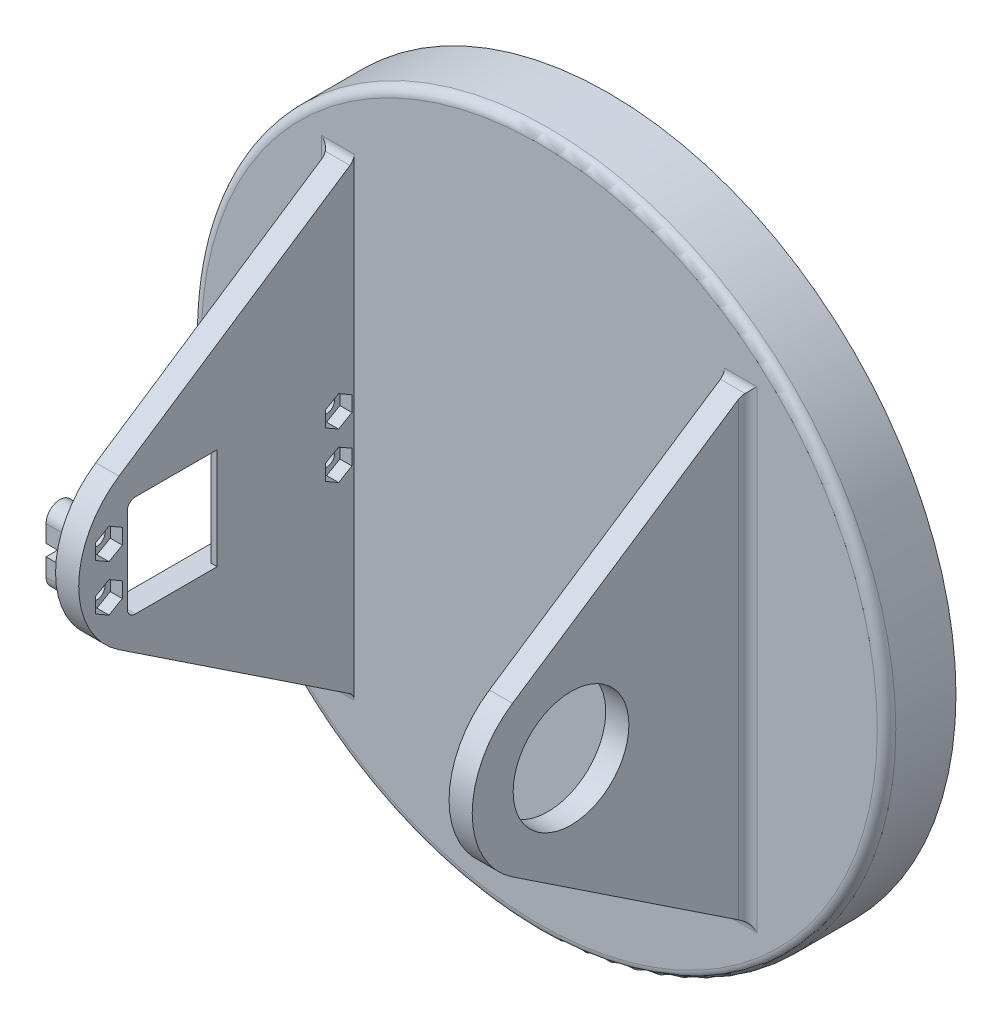
SolidWorks part; units mm, degrees
ref_plane "Front Plane" through (0, 0, 0) normal (0, 0, 1) x (1, 0, 0)
ref_plane "Top Plane" through (0, 0, 0) normal (0, 1, 0) x (1, 0, 0)
ref_plane "Right Plane" through (0, 0, 0) normal (1, 0, 0) x (0, 0, -1)
sketch "Sketch1" plane through (0, 0, 0) normal (0, 0, 1) x (1, 0, 0)
  circle A0 centre (0, 0) radius 75
  dimension "D1" = 150
extrude "Base Plate\\" add sketch "Sketch1" along normal blind 15
sketch "Sketch2" plane through (0, 0, 0) normal (0, 0, -1) x (-1, 0, 0)
  circle A0 centre (0, 0) radius 25 construction
  circle A1 centre (0, -25) radius 4.5
  circle A2 centre (-23.7764, -7.7254) radius 4.5
  circle A3 centre (-14.6946, 20.2254) radius 4.5
  circle A4 centre (14.6946, 20.2254) radius 4.5
  circle A5 centre (23.7764, -7.7254) radius 4.5
  point P16 (0, 0)
  dimension "D2" = 9
  dimension "D3" = 50
  dimension "D1" = 5
extrude "Drive Holes" cut sketch "Sketch2" against normal blind 10
chamfer "Chamfer1" distance 1 5 edges at (19.2764, -7.7254, 0) (10.1946, 20.2254, 0) (-19.1946, 20.2254, 0) (-28.2764, -7.7254, 0) (-4.5, -25, 0)
sketch "Sketch4" plane through (0, 0, 0) normal (1, 0, 0) x (0, 0, -1)
  line L0 (-15, 50) -> (-65.792, 16.2334)
  line L1 (-15, 75) -> (-15, -75) construction
  line L2 (-65.792, -16.2334) -> (-15, -50)
  line L3 (-15, -50) -> (-15, 50)
  arc A0 (-65.792, 16.2334) -> (-65.792, -16.2334) centre (-55, 0) ccw
  dimension "D1" = 100
  dimension "D2" = 40
extrude "Base Fin" add sketch "Sketch4" against normal blind 5 from offset 45
sketch "Sketch5" plane through (40, 0, 0) normal (-1, 0, 0) x (0, 0, 1)
  line L0 (15, 50) -> (15, -50)
  line L1 (15, -50) -> (65.792, -16.2334)
  line L2 (65.792, 16.2334) -> (15, 50)
  arc A0 (65.792, -16.2334) -> (65.792, 16.2334) centre (55, 0) ccw
extrude "Base Fin 2" add sketch "Sketch5" against normal blind 5 from offset 85
sketch "Sketch6" plane through (-45, 0, 0) normal (-1, 0, 0) x (0, 0, 1)
  line L0 (64, 8.8325) -> (64, -9.5675)
  line L1 (62.25, -11.3175) -> (24.05, -11.3175)
  line L2 (22.3, -9.5675) -> (22.3, 8.8325)
  line L3 (24.05, 10.5825) -> (62.25, 10.5825)
  arc A0 (64, -9.5675) -> (62.25, -11.3175) centre (62.25, -9.5675) cw
  arc A1 (24.05, -11.3175) -> (22.3, -9.5675) centre (24.05, -9.5675) cw
  arc A2 (22.3, 8.8325) -> (24.05, 10.5825) centre (24.05, 8.8325) cw
  arc A3 (62.25, 10.5825) -> (64, 8.8325) centre (62.25, 8.8325) cw
extrude "Cut-Extrude1" cut sketch "Sketch6" against normal up to next
sketch "Sketch7" plane through (-45, 0, 0) normal (-1, 0, 0) x (0, 0, 1)
  circle A0 centre (18.35, 4.6325) radius 1.75
  circle A1 centre (18.35, -5.3675) radius 1.75
  circle A2 centre (67.95, -5.3675) radius 1.75
  circle A3 centre (67.95, 4.6325) radius 1.75
  dimension "D1" = 3.5
extrude "Cut-Extrude2" cut sketch "Sketch7" against normal up to next
sketch "Sketch8" plane through (-45, 0, 0) normal (-1, 0, 0) x (0, 0, 1)
  line L0 (67.95, 4.6325) -> (67.95, -5.3675) construction
  line L1 (70.95, 4.6325) -> (70.95, -5.3675)
  line L2 (64.95, 4.6325) -> (64.95, -5.3675)
  line L3 (15, 7.6325) -> (15, 0)
  line L4 (15, -75) -> (15, 75) construction
  line L5 (15, 0) -> (15, -8.3675)
  line L6 (15, -8.3675) -> (18.35, -8.3675)
  line L7 (21.35, -5.3675) -> (21.35, 4.6325)
  line L8 (18.35, 7.6325) -> (15, 7.6325)
  arc A0 (70.95, 4.6325) -> (64.95, 4.6325) centre (67.95, 4.6325) ccw
  arc A1 (64.95, -5.3675) -> (70.95, -5.3675) centre (67.95, -5.3675) ccw
  arc A2 (18.35, -8.3675) -> (21.35, -5.3675) centre (18.35, -5.3675) ccw
  arc A3 (21.35, 4.6325) -> (18.35, 7.6325) centre (18.35, 4.6325) ccw
  circle A4 centre (18.35, 4.6325) radius 1.75 construction
  circle A5 centre (18.35, -5.3675) radius 1.75 construction
  point P4 (67.95, -0.3675)
  dimension "D1" = 3
  dimension "D2" = 3
extrude "Boss-Extrude1" add sketch "Sketch8" along normal up to surface (5.6 mm away)
sketch "Sketch9" plane through (-45, 0, 0) normal (1, 0, 0) x (0, 0, -1)
  circle A0 centre (-67.95, -5.3675) radius 1.75
  circle A1 centre (-67.95, 4.6325) radius 1.75
  circle A2 centre (-18.35, -5.3675) radius 1.75
  circle A3 centre (-18.35, 4.6325) radius 1.75
extrude "Cut-Extrude3" cut sketch "Sketch9" against normal up to surface (5.6 mm away) up to face at (-50.6, -0.3675, 18.4404)
sketch "Sketch10" plane through (-50.6, 0, 0) normal (-1, 0, 0) x (0, 0, 1)
  line L0 (21.35, 0.8825) -> (16.75, 0.8825)
  line L1 (21.35, 4.6325) -> (21.35, -5.3675) construction
  line L2 (16.75, 0.8825) -> (16.75, -1.6175)
  line L3 (16.75, -1.6175) -> (21.35, -1.6175)
  line L4 (23.05, 0.3825) -> (17.25, 0.3825) construction
  line L5 (17.25, -1.1175) -> (23.05, -1.1175) construction
  line L6 (17.25, 0.3825) -> (17.25, -1.1175) construction
  line L7 (21.35, 0.8825) -> (21.35, -1.6175)
  line L10 (64.95, -5.3675) -> (64.95, 4.6325) construction
  line L14 (64.95, -1.5747) -> (64.95, 0.9253)
  line L22 (64.95, 0.9253) -> (70.95, 0.9253)
  line L23 (70.95, 4.6325) -> (70.95, -5.3675) construction
  line L24 (70.95, 0.9253) -> (70.95, -1.5747)
  line L25 (70.95, -1.5747) -> (64.95, -1.5747)
  dimension "D1" = 0.5
  dimension "D2" = 0.5
  dimension "D3" = 0.5
extrude "Cut-Extrude4" cut sketch "Sketch10" against normal up to surface (5.6 mm away) up to face at (-45, -0.2205, 28.0928)
sketch "Sketch11" plane through (-40, 0, 0) normal (1, 0, 0) x (0, 0, -1)
  line L1 (-65.075, -7.0274) -> (-65.075, -3.7076)
  line L2 (-65.075, -3.7076) -> (-67.95, -2.0477)
  line L3 (-67.95, -2.0477) -> (-70.825, -3.7076)
  line L4 (-70.825, -3.7076) -> (-70.825, -7.0274)
  line L5 (-70.825, -7.0274) -> (-67.95, -8.6873)
  line L6 (-67.95, -8.6873) -> (-65.075, -7.0274)
  line L7 (-65.075, 2.9726) -> (-65.075, 6.2924)
  line L8 (-65.075, 6.2924) -> (-67.95, 7.9523)
  line L9 (-67.95, 7.9523) -> (-70.825, 6.2924)
  line L10 (-70.825, 6.2924) -> (-70.825, 2.9726)
  line L11 (-70.825, 2.9726) -> (-67.95, 1.3127)
  line L12 (-67.95, 1.3127) -> (-65.075, 2.9726)
  line L13 (-15.475, -7.0274) -> (-15.475, -3.7076)
  line L14 (-15.475, -3.7076) -> (-18.35, -2.0477)
  line L15 (-18.35, -2.0477) -> (-21.225, -3.7076)
  line L16 (-21.225, -3.7076) -> (-21.225, -7.0274)
  line L17 (-21.225, -7.0274) -> (-18.35, -8.6873)
  line L18 (-18.35, -8.6873) -> (-15.475, -7.0274)
  line L19 (-15.475, 2.9726) -> (-15.475, 6.2924)
  line L20 (-15.475, 6.2924) -> (-18.35, 7.9523)
  line L21 (-18.35, 7.9523) -> (-21.225, 6.2924)
  line L22 (-21.225, 6.2924) -> (-21.225, 2.9726)
  line L23 (-21.225, 2.9726) -> (-18.35, 1.3127)
  line L24 (-18.35, 1.3127) -> (-15.475, 2.9726)
  circle A0 centre (-67.95, -5.3675) radius 2.875 construction
  circle A1 centre (-67.95, 4.6325) radius 2.875 construction
  circle A2 centre (-18.35, -5.3675) radius 2.875 construction
  circle A3 centre (-18.35, 4.6325) radius 2.875 construction
  circle A4 centre (-18.35, 4.6325) radius 1.75 construction
  dimension "D1" = 5.75
extrude "Cut-Extrude5" cut sketch "Sketch11" against normal blind 2.6
sketch "Sketch12" plane through (-40, 0, 0) normal (1, 0, 0) x (0, 0, -1)
  line L0 (-44.5721, -11.3175) -> (-44.5721, 10.5825)
  line L1 (-62.25, -11.3175) -> (-24.05, -11.3175) construction
  line L2 (-24.05, 10.5825) -> (-62.25, 10.5825) construction
  line L3 (-44.5721, 10.5825) -> (-24.05, 10.5825)
  line L4 (-22.3, 8.8325) -> (-22.3, -9.5675)
  line L5 (-24.05, -11.3175) -> (-44.5721, -11.3175)
  arc A0 (-24.05, 10.5825) -> (-22.3, 8.8325) centre (-24.05, 8.8325) cw
  arc A1 (-22.3, -9.5675) -> (-24.05, -11.3175) centre (-24.05, -9.5675) cw
extrude "Boss-Extrude2" add sketch "Sketch12" against normal up to surface (1.38 mm away)
fillet "Fillet1" radius 2 9 edges at (42.5, -50, 15) (42.5, 50, 15) (45, 0, 15) (-47.8, 7.6325, 15) (-47.8, -8.3675, 15) (-42.5, -50, 15) (-42.5, 50, 15) (-45, -29.1838, 15) (-45, 28.8162, 15)
fillet "Fillet2" radius 2 1 edges at (75, 0, 15)
sketch "Sketch13" plane through (40, 0, 0) normal (-1, 0, 0) x (0, 0, 1)
  circle A0 centre (53.15, -0.3675) radius 12.5
  arc A1 (59.7219, 18.5219) -> (46.5781, -19.2569) centre (53.15, -0.3675) ccw construction
  dimension "D1" = 25
extrude "Cut-Extrude6" cut sketch "Sketch13" against normal up to next
